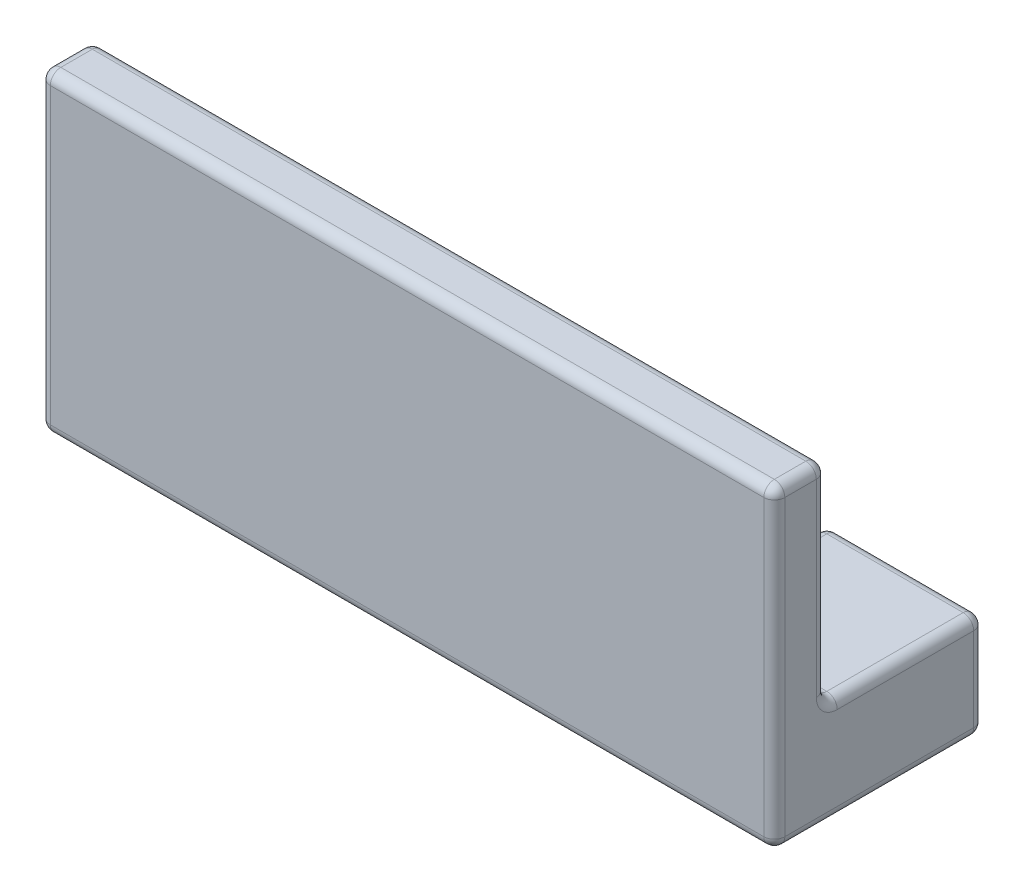
SolidWorks part; units mm, degrees
ref_plane "Front Plane" through (0, 0, 0) normal (0, 0, 1) x (1, 0, 0)
ref_plane "Top Plane" through (0, 0, 0) normal (0, 1, 0) x (1, 0, 0)
ref_plane "Right Plane" through (0, 0, 0) normal (1, 0, 0) x (0, 0, -1)
sketch "Sketch1" plane through (0, 0, 0) normal (0, 1, 0) x (1, 0, 0)
  line L1 (0, 0) -> (70, 0)
  line L2 (0, 0) -> (0, 5)
  line L3 (0, 5) -> (70, 5)
  line L4 (70, 0) -> (70, 5)
extrude "Boss-Extrude1" add sketch "Sketch1" along normal blind 30
sketch "Sketch4" plane through (0, 0, 0) normal (0, -1, 0) x (-1, 0, 0)
  line L1 (-70, 5) -> (0, 5)
  line L2 (-70, 5) -> (-70, 20)
  line L3 (-70, 20) -> (0, 20)
  line L4 (0, 5) -> (0, 20)
extrude "Boss-Extrude2" add sketch "Sketch4" against normal blind 10 contours L3 L4 L1 L2
sketch "Sketch5" plane through (0, 10, 0) normal (0, 1, 0) x (1, 0, 0)
  line L0 (70, 20) -> (0, 20) construction
  line L1 (15, 20) -> (19, 20)
  line L2 (15, 20) -> (15, 10)
  line L3 (15, 10) -> (19, 10)
  line L4 (19, 20) -> (19, 10)
  line L5 (70, 20) -> (0, 20) construction
  line L6 (19.9862, 20) -> (20.417, 20)
  line L7 (19.9862, 20) -> (19.9862, 10)
  line L8 (19.9862, 10) -> (20.417, 10)
  line L9 (20.417, 20) -> (20.417, 10)
  point P12 (54.4643, -40.8373)
extrude "Cut-Extrude1" cut sketch "Sketch5" against normal blind 10 contours L2 L3 L4 L1
sketch "Sketch6" plane through (0, 10, 0) normal (0, 1, 0) x (1, 0, 0)
  line L0 (70, 20) -> (19, 20) construction
  line L1 (27, 20) -> (31, 20)
  line L2 (27, 20) -> (27, 10)
  line L3 (27, 10) -> (31, 10)
  line L4 (31, 20) -> (31, 10)
extrude "Cut-Extrude2" cut sketch "Sketch6" against normal blind 10
sketch "Sketch7" plane through (0, 10, 0) normal (0, 1, 0) x (1, 0, 0)
  line L0 (70, 20) -> (31, 20) construction
  line L1 (39, 20) -> (43, 20)
  line L2 (39, 20) -> (39, 10)
  line L3 (39, 10) -> (43, 10)
  line L4 (43, 20) -> (43, 10)
extrude "Cut-Extrude3" cut sketch "Sketch7" against normal blind 10
sketch "Sketch8" plane through (0, 10, 0) normal (0, 1, 0) x (1, 0, 0)
  line L0 (70, 20) -> (43, 20) construction
  line L1 (51, 20) -> (55, 20)
  line L2 (51, 20) -> (51, 10)
  line L3 (51, 10) -> (55, 10)
  line L4 (55, 20) -> (55, 10)
extrude "Cut-Extrude4" cut sketch "Sketch8" against normal blind 10
fillet "Fillet5" radius 1 58 edges at (43, 0, -15) (41, 0, -10) (39, 0, -15) (31, 0, -15) (29, 0, -10) (27, 0, -15) (19, 0, -15) (17, 0, -10) (15, 0, -15) (55, 0, -15) (53, 0, -10) (51, 0, -15) (0, 0, -10) (0, 15, 0) (35, 0, 0) (0, 5, -20) (7.5, 10, -20) (7.5, 0, -20) (15, 5, -20) (19, 5, -20) (23, 10, -20) (23, 0, -20) (27, 5, -20) (31, 5, -20) (35, 10, -20) (35, 0, -20) (39, 5, -20) (43, 5, -20) (47, 10, -20) (47, 0, -20) (51, 5, -20) (55, 5, -20) (62.5, 10, -20) (62.5, 0, -20) (53, 10, -10) (55, 10, -15) (0, 10, -12.5) (15, 10, -15) (17, 10, -10) (19, 10, -15) (27, 10, -15) (29, 10, -10) (31, 10, -15) (39, 10, -15) (41, 10, -10) (43, 10, -15) (51, 10, -15) (70, 15, 0) (70, 10, -12.5) (70, 5, -20) (70, 0, -10) (70, 30, -2.5) (35, 30, 0) (0, 30, -2.5) (35, 30, -5) (0, 20, -5) (35, 10, -5) (70, 20, -5)
